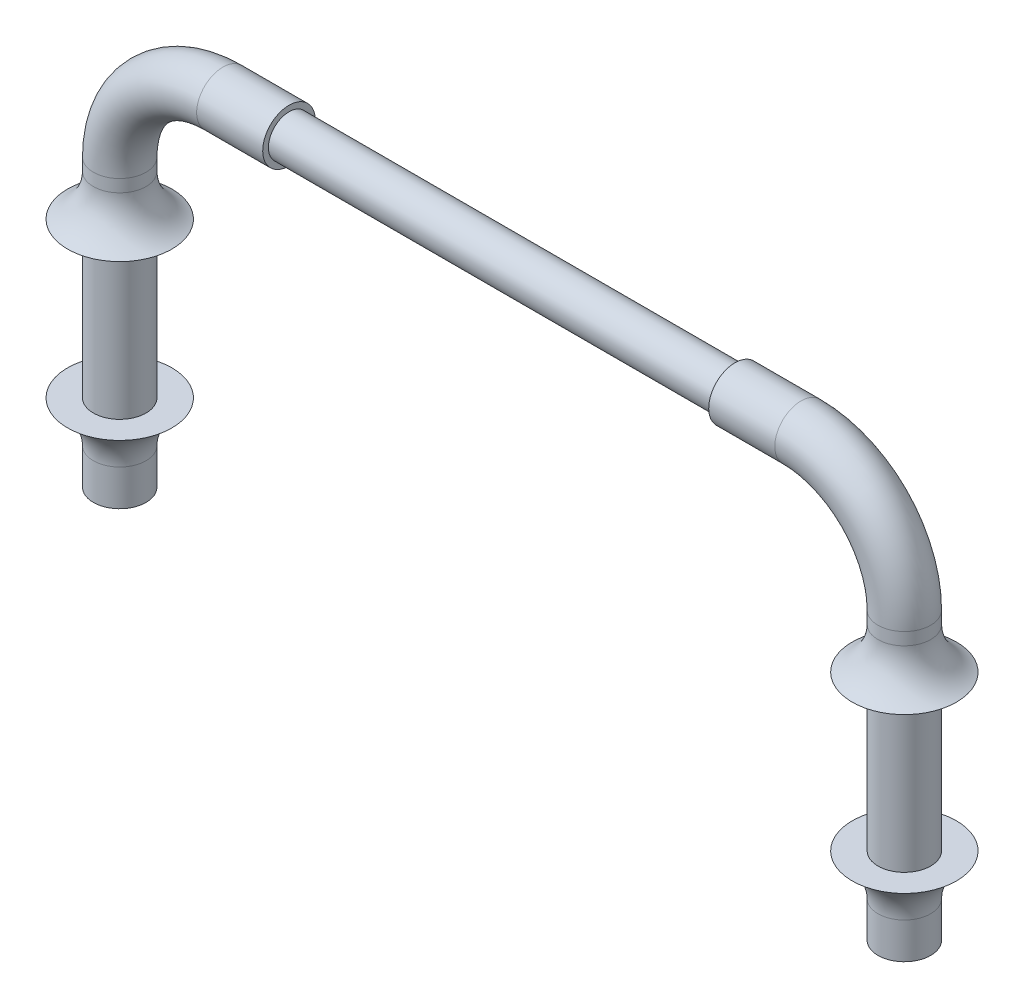
SolidWorks part; units mm, degrees
ref_plane "Front Plane" through (0, 0, 0) normal (0, 0, 1) x (1, 0, 0)
ref_plane "Top Plane" through (0, 0, 0) normal (0, 1, 0) x (1, 0, 0)
ref_plane "Right Plane" through (0, 0, 0) normal (1, 0, 0) x (0, 0, -1)
sketch "Sketch1" plane through (0, 0, 0) normal (0, 1, 0) x (1, 0, 0)
  circle A0 centre (0, 0) radius 0.255
  dimension "D1" = 0.51
extrude "Extrude1" add sketch "Sketch1" against normal blind 2
sketch "Sketch2" plane through (0, 0, 0) normal (0, 1, 0) x (1, 0, 0)
  circle A1 centre (0, 0) radius 0.255
  circle A2 centre (0, 0) radius 0.255
  dimension "D1" = 0
extrude "Extrude2" add sketch "Sketch2" along normal blind 0.77
sketch "Sketch3" plane through (0, 0.77, 0) normal (0, 1, 0) x (1, 0, 0)
  line L0 (1, 0.255) -> (1, -0.255) construction
  circle A1 centre (0, 0) radius 0.255
  circle A2 centre (0, 0) radius 0.255
  dimension "D2" = 1
  dimension "D1" = 0
revolve "Revolve1" add sketch "Sketch3" angle 90 about L0
sketch "Sketch4" plane through (1, 0, 0) normal (1, 0, 0) x (0, 0, -1)
  circle A2 centre (0, 1.77) radius 0.255
  circle A3 centre (0, 1.77) radius 0.255
  dimension "D1" = 0
extrude "Extrude4" add sketch "Sketch4" along normal blind 0.64
sketch "Sketch6" plane through (1.64, 0, 0) normal (1, 0, 0) x (0, 0, -1)
  circle A0 centre (0, 1.77) radius 0.2
  dimension "D1" = 0.4
extrude "Extrude5" add sketch "Sketch6" along normal blind 4.32
sketch "Sketch7" plane through (5.96, 0, 0) normal (1, 0, 0) x (0, 0, -1)
  circle A0 centre (0, 1.77) radius 0.255
  circle A1 centre (0, 1.77) radius 0.255 construction
extrude "Extrude6" add sketch "Sketch7" along normal blind 0.64
sketch "Sketch8" plane through (6.6, 0, 0) normal (1, 0, 0) x (0, 0, -1)
  line L0 (-0.255, 0.77) -> (0.255, 0.77) construction
  line L1 (-0.255, 1.77) -> (-0.255, 0.77) construction
  line L2 (0.255, 0.77) -> (0.255, 1.77) construction
  circle A1 centre (0, 1.77) radius 0.255
  circle A2 centre (0, 1.77) radius 0.255
  dimension "D2" = 1
  dimension "D1" = 0
revolve "Revolve3" add sketch "Sketch8" angle 90 about L0
sketch "Sketch9" plane through (0, 0.77, 0) normal (0, -1, 0) x (1, 0, 0)
  circle A1 centre (7.6, 0) radius 0.255
  circle A2 centre (7.6, 0) radius 0.255
  dimension "D1" = 0
extrude "Extrude7" add sketch "Sketch9" along normal up to surface (2.77 mm away) up to face at (0, -2, 0.255)
sketch "Sketch10" plane through (0, 0, 0) normal (0, 0, 1) x (1, 0, 0)
  line L0 (-2.5606, 0.25) -> (9.9425, 0.25) construction
  line L1 (9.9425, 0.25) -> (9.9425, -1.25) construction
  line L2 (9.9425, -1.25) -> (-2.5606, -1.25) construction
  line L3 (-2.5606, -1.25) -> (-2.5606, 0.25) construction
  line L4 (1.64, 3.04) -> (1.64, 0.5) construction
  line L5 (1.64, 0.5) -> (5.96, 0.5) construction
  line L6 (5.96, 0.5) -> (5.96, 3.04) construction
  line L7 (5.96, 3.04) -> (1.64, 3.04) construction
  line L8 (1.64, 1.515) -> (1.64, 2.025) construction
  line L9 (5.96, 2.025) -> (5.96, 1.515) construction
  line L10 (1, 1.77) -> (6.6, 1.77) construction
  line L11 (1, 1.515) -> (1, 2.025) construction
  line L12 (6.6, 2.025) -> (6.6, 1.515) construction
  line L13 (0, -2) -> (0, 0.77) construction
  line L14 (-0.255, -2) -> (0.255, -2) construction
  line L15 (0.255, 0.77) -> (-0.255, 0.77) construction
  line L16 (-0.255, 0.25) -> (-0.255, 0.65)
  line L19 (-0.255, -1.25) -> (-0.505, -1.25)
  line L20 (-0.255, 0.25) -> (-0.505, 0.25)
  line L21 (-0.255, 0.77) -> (-0.255, -2) construction
  line L22 (-0.255, -1.25) -> (-0.255, -1.65)
  arc A0 (-0.505, 0.25) -> (-0.255, 0.65) centre (-0.7, 0.65) ccw
  arc A1 (-0.255, -1.65) -> (-0.505, -1.25) centre (-0.7, -1.65) ccw
  dimension "D1" = 1.5
  dimension "D2" = 1.27
  dimension "D3" = 1.27
  dimension "D4" = 0.25
  dimension "D5" = 0.25
  dimension "D6" = 0.25
  dimension "D7" = 0.4
  dimension "D8" = 0.4
revolve "Revolve4" add sketch "Sketch10" angle 360 about L13
sketch "Sketch11" plane through (0, 0, 0) normal (0, 0, 1) x (1, 0, 0)
  line L0 (7.855, 0.25) -> (8.105, 0.25)
  line L1 (7.855, -2) -> (7.855, 0.77) construction
  line L2 (7.855, -1.25) -> (8.105, -1.25)
  line L3 (-0.255, 0.25) -> (0.255, 0.25) construction
  line L4 (0.505, -1.25) -> (-0.505, -1.25) construction
  line L5 (7.6, -2) -> (7.6, 0.77) construction
  line L6 (7.345, -2) -> (7.855, -2) construction
  line L7 (7.855, 0.77) -> (7.345, 0.77) construction
  line L8 (7.855, -1.25) -> (7.855, -1.65)
  line L9 (7.855, 0.25) -> (7.855, 0.65)
  arc A0 (8.105, 0.25) -> (7.855, 0.65) centre (8.3, 0.65) cw
  arc A1 (8.105, -1.25) -> (7.855, -1.65) centre (8.3, -1.65) ccw
  dimension "D1" = 0.25
  dimension "D2" = 0.4
  dimension "D3" = 0.4
revolve "Revolve5" add sketch "Sketch11" angle 360 about L5
